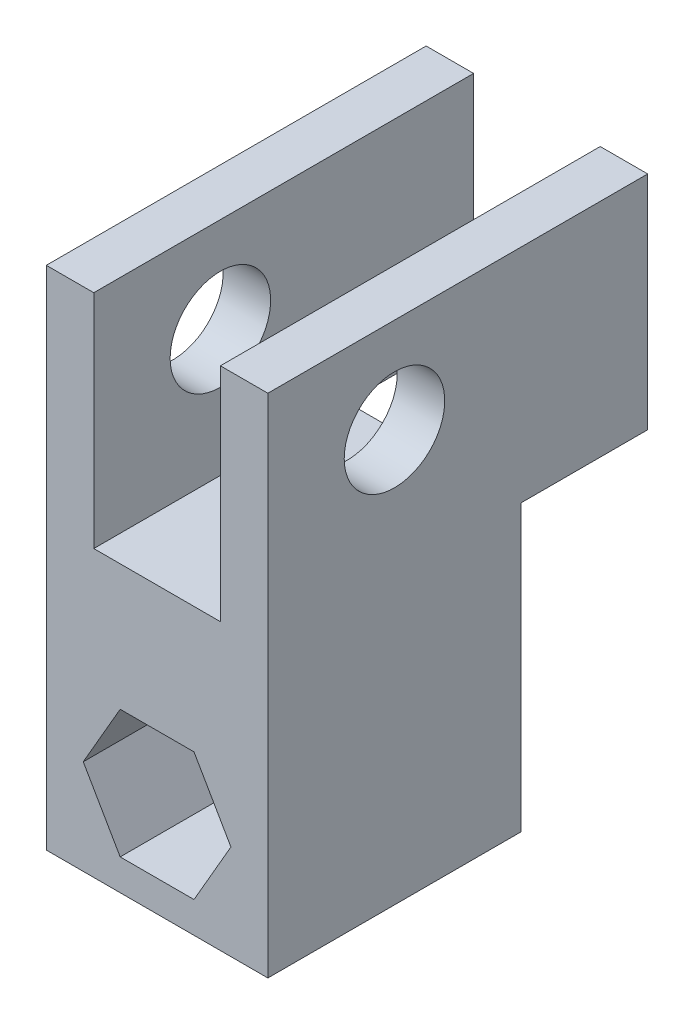
SolidWorks part; units mm, degrees
material "6061-T6 (SS)"
ref_plane "Front" through (0, 0, 0) normal (0, 0, 1) x (1, 0, 0)
ref_plane "Top" through (0, 0, 0) normal (0, 1, 0) x (1, 0, 0)
ref_plane "Right" through (0, 0, 0) normal (1, 0, 0) x (0, 0, -1)
sketch "Sketch1" plane through (0, 0, 0) normal (0, 0, 1) x (1, 0, 0)
  line L0 (-11.1125, 0) -> (11.1125, 0)
  line L1 (-11.1125, 0) -> (-11.1125, 50.8)
  line L2 (-11.1125, 50.8) -> (-6.35, 50.8)
  line L3 (-6.35, 50.8) -> (-6.35, 28.575)
  line L4 (-6.35, 28.575) -> (6.35, 28.575)
  line L5 (6.35, 28.575) -> (6.35, 50.8)
  line L6 (6.35, 50.8) -> (11.1125, 50.8)
  line L7 (11.1125, 50.8) -> (11.1125, 0)
  point P4 (0, 0)
  dimension "D1" = 22.225
  dimension "D2" = 50.8
  dimension "D3" = 12.7
  dimension "D4" = 22.225
extrude "Boss-Extrude1" add sketch "Sketch1" along normal blind 25.4
sketch "Sketch2" plane through (0, 0, 25.4) normal (0, 0, 1) x (1, 0, 0)
  line L0 (0, 0) -> (0, 3.1115) construction
  line L1 (3.7028, 15.9385) -> (-3.7028, 15.9385)
  line L2 (-3.7028, 15.9385) -> (-7.4057, 9.525)
  line L3 (-7.4057, 9.525) -> (-3.7028, 3.1115)
  line L4 (-3.7028, 3.1115) -> (3.7028, 3.1115)
  line L5 (3.7028, 3.1115) -> (7.4057, 9.525)
  line L6 (7.4057, 9.525) -> (3.7028, 15.9385)
  line L7 (-11.1125, 0) -> (11.1125, 0) construction
  circle A0 centre (0, 9.525) radius 6.4135 construction
  dimension "D1" = 12.827
  dimension "D2" = 9.525
extrude "Cut-Extrude1" cut sketch "Sketch2" against normal through all
sketch "Sketch6" plane through (-11.1125, 0, 0) normal (-1, 0, 0) x (0, 0, 1)
  line L0 (25.4, 50.8) -> (0, 50.8) construction
  line L2 (12.7, 41.275) -> (25.4, 41.275) construction
  line L3 (25.4, 50.8) -> (25.4, 0) construction
  line L5 (12.7, 41.275) -> (0, 41.275) construction
  line L6 (0, 50.8) -> (0, 0) construction
  point P0 (12.7, 41.275)
  dimension "D1" = 9.525
hole_wizard "3/8 Clearance Hole1" positions "Sketch6" profile "Sketch4" hole size "3/8" standard "ANSI Inch" end condition through all
sketch "Sketch4" plane through (-11.1125, 41.275, 12.7) normal (0, 1, 0) x (0, 0, 1)
  line L0 (0, 0) -> (0, 22.225)
  line L1 (0, 22.225) -> (5.0419, 22.225)
  line L2 (5.0419, 22.225) -> (5.0419, 0)
  line L5 (5.0419, 0) -> (0, 0)
  line L11 (0, -6.35) -> (0, 107.95) construction
  dimension "Thru Hole Dia." = 10.0838
  dimension "Thru Hole Depth" = 22.225
sketch "Sketch7" plane through (0, 0, 0) normal (0, 0, -1) x (-1, 0, 0)
  line L1 (-11.1125, 50.8) -> (-6.35, 50.8)
  line L2 (-11.1125, 50.8) -> (-11.1125, 28.575)
  line L3 (-11.1125, 28.575) -> (-6.35, 28.575)
  line L4 (-6.35, 50.8) -> (-6.35, 28.575)
  line L5 (11.1125, 50.8) -> (6.35, 50.8)
  line L6 (11.1125, 50.8) -> (11.1125, 28.575)
  line L7 (11.1125, 28.575) -> (6.35, 28.575)
  line L8 (6.35, 50.8) -> (6.35, 28.575)
extrude "Boss-Extrude2" add sketch "Sketch7" along normal blind 12.7
